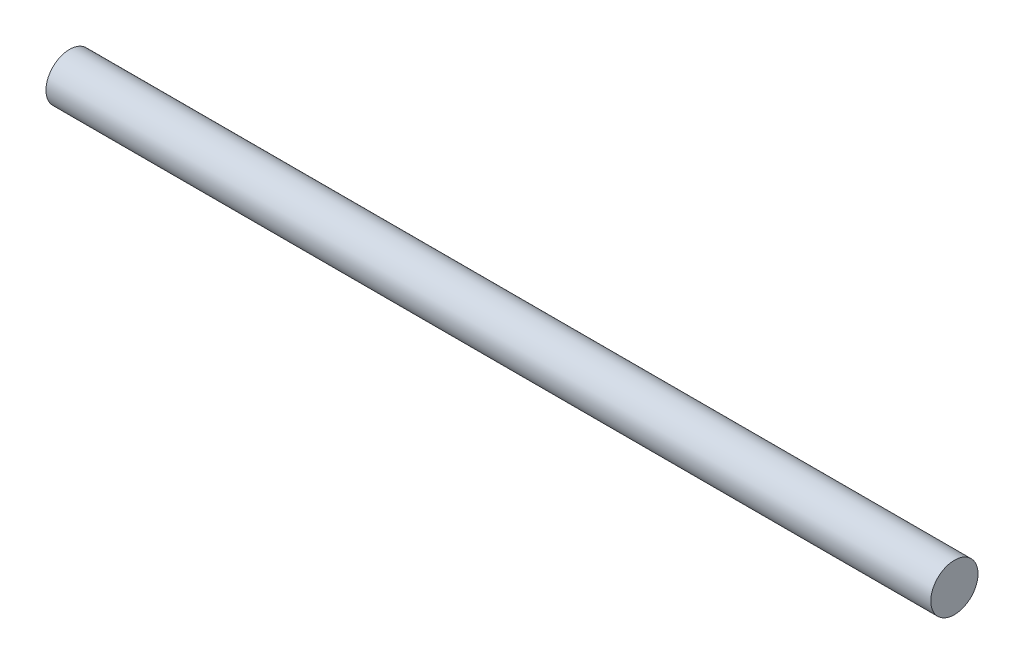
SolidWorks part; units mm, degrees
material "AISI 304"
ref_plane "Front Plane" through (0, 0, 0) normal (0, 0, 1) x (1, 0, 0)
ref_plane "Top Plane" through (0, 0, 0) normal (0, 1, 0) x (1, 0, 0)
ref_plane "Right Plane" through (0, 0, 0) normal (1, 0, 0) x (0, 0, -1)
sketch "Schizzo1" plane through (0, 0, 0) normal (1, 0, 0) x (0, 0, -1)
  circle A0 centre (0, 0) radius 2
  dimension "D1" = 4
extrude "Estrusione-Estrusione1" add sketch "Schizzo1" along normal blind 75
sketch "Schizzo2" plane through (0, 0, 0) normal (0, 0, -1) x (-1, 0, 0)
  line L0 (-1.355, 2) -> (-1.785, 2)
  line L1 (-1.785, 2) -> (-1.57, 1.57)
  line L2 (-1.57, 1.57) -> (-1.355, 2)
  line L6 (0, 2) -> (-75, 2) construction
  dimension "D1" = 0.43
  dimension "D2" = 0.43
